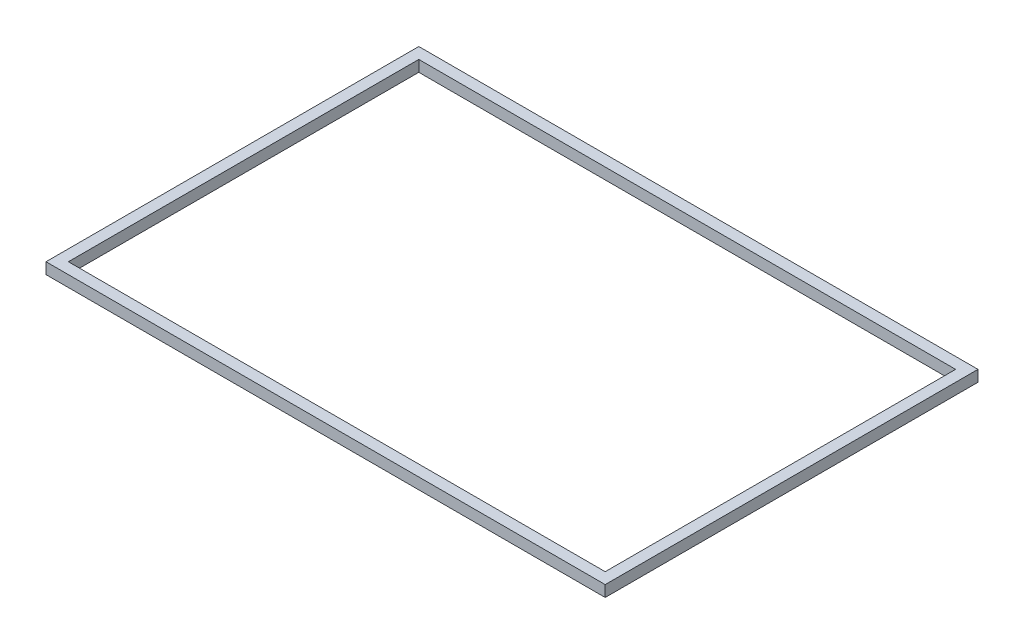
SolidWorks part; units mm, degrees
ref_plane "Front Plane" through (0, 0, 0) normal (0, 0, 1) x (1, 0, 0)
ref_plane "Top Plane" through (0, 0, 0) normal (0, 1, 0) x (1, 0, 0)
ref_plane "Right Plane" through (0, 0, 0) normal (1, 0, 0) x (0, 0, -1)
sketch "Sketch2" plane through (0, 0, 0) normal (0, 1, 0) x (1, 0, 0)
  line L0 (3, 3) -> (3, 97)
  line L1 (0, 0) -> (150, 0)
  line L2 (0, 0) -> (0, 100)
  line L3 (0, 100) -> (150, 100)
  line L4 (150, 0) -> (150, 100)
  line L5 (3, 97) -> (147, 97)
  line L6 (147, 3) -> (147, 97)
  line L7 (3, 3) -> (147, 3)
  point P9 (0, 0)
  dimension "D1" = 3
extrude "Boss-Extrude1" add sketch "Sketch2" along normal blind 3 contours L1 L4 L3 L2 L7 L0 L5 L6
